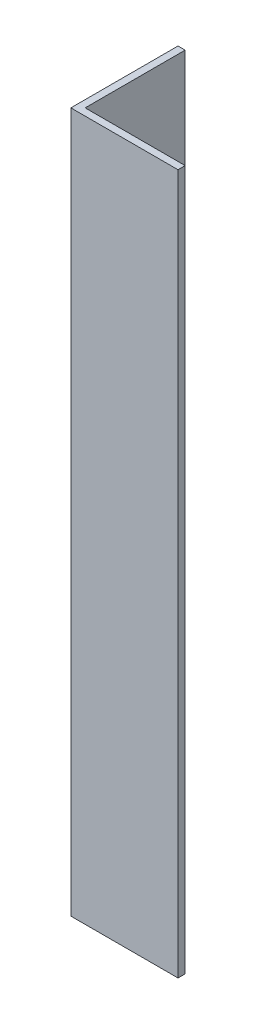
SolidWorks part; units mm, degrees
material "1060 Сплав"
ref_plane "Спереди" through (0, 0, 0) normal (0, 0, 1) x (1, 0, 0)
ref_plane "Сверху" through (0, 0, 0) normal (0, 1, 0) x (1, 0, 0)
ref_plane "Справа" through (0, 0, 0) normal (1, 0, 0) x (0, 0, -1)
sketch "Эскиз1" plane through (0, 0, 0) normal (0, 1, 0) x (1, 0, 0)
  line L0 (0, 0) -> (0, 15)
  line L1 (0, 15) -> (1, 15)
  line L2 (1, 15) -> (1, 1)
  line L3 (1, 1) -> (15, 1)
  line L4 (15, 1) -> (15, 0)
  line L5 (15, 0) -> (0, 0)
  dimension "D1" = 1
  dimension "D2" = 15
extrude "Бобышка-Вытянуть1" add sketch "Эскиз1" along normal blind 98
sketch "Эскиз2" plane through (0, 0, 0) normal (-1, 0, 0) x (0, 0, 1)
  line L0 (-7.5, 98) -> (-7.5, 0) construction
  line L1 (-15, 98) -> (0, 98) construction
  line L2 (-15, 0) -> (0, 0) construction
